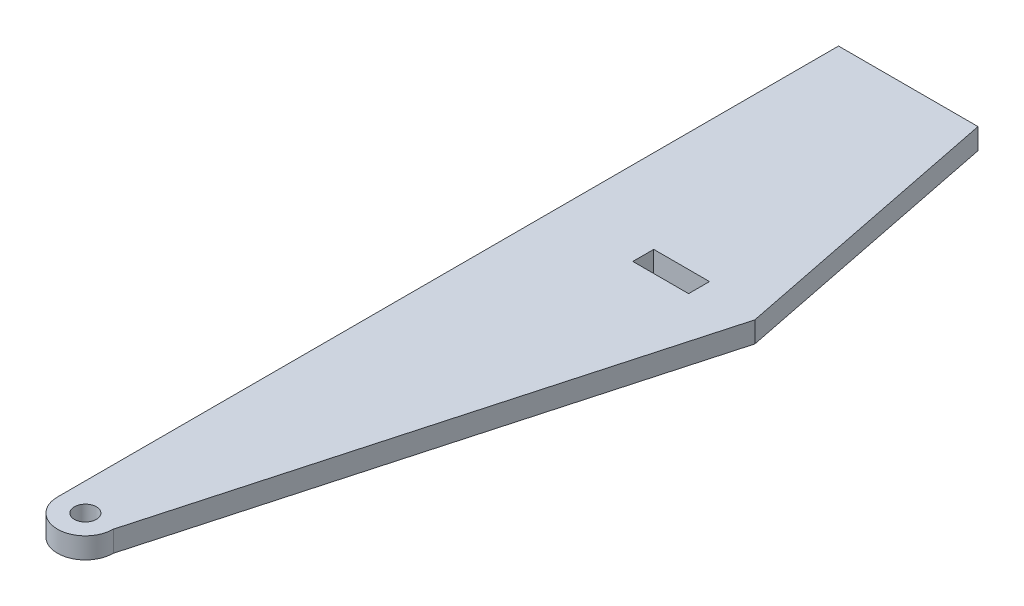
SolidWorks part; units mm, degrees
material "Pine"
ref_plane "Front Plane" through (0, 0, 0) normal (0, 0, 1) x (1, 0, 0)
ref_plane "Top Plane" through (0, 0, 0) normal (0, 1, 0) x (1, 0, 0)
ref_plane "Right Plane" through (0, 0, 0) normal (1, 0, 0) x (0, 0, -1)
sketch "Sketch1" plane through (0, 0, 0) normal (0, 1, 0) x (1, 0, 0)
  line L0 (-25.4, 0) -> (-25.4, 711.2)
  line L1 (-25.4, 711.2) -> (101.6, 711.2)
  line L2 (101.6, 711.2) -> (152.4, 457.2)
  line L3 (152.4, 457.2) -> (25.4, 0)
  line L4 (152.4, 457.2) -> (-25.4, 457.2) construction
  line L6 (50.8, 447.675) -> (101.6, 447.675)
  line L7 (50.8, 447.675) -> (50.8, 466.725)
  line L8 (50.8, 466.725) -> (101.6, 466.725)
  line L9 (101.6, 447.675) -> (101.6, 466.725)
  line L10 (50.8, 447.675) -> (101.6, 466.725) construction
  line L11 (50.8, 466.725) -> (101.6, 447.675) construction
  circle A0 centre (0, 0) radius 10
  arc A1 (-25.4, 0) -> (25.4, 0) centre (0, 0) ccw
  point P5 (76.2, 457.2)
  dimension "D1" = 20
  dimension "D2" = 177.8
  dimension "D3" = 711.2
  dimension "D4" = 0
  dimension "D5" = 0
  dimension "D6" = 127
  dimension "D7" = 254
  dimension "D8" = 50.8
  dimension "D9" = 50.8
  dimension "D10" = 19.05
  dimension "D11" = 76.2
extrude "Boss-Extrude1" add sketch "Sketch1" along normal blind 19.05
